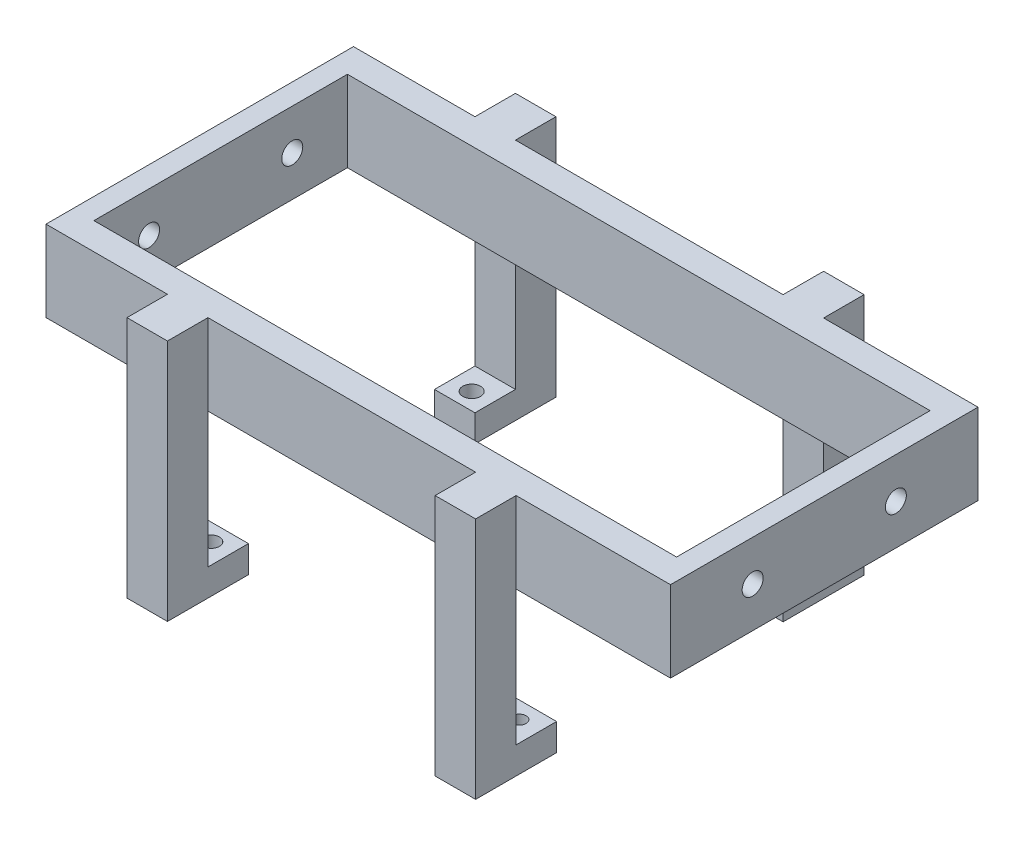
SolidWorks part; units mm, degrees
material "ABS"
ref_plane "Front Plane" through (0, 0, 0) normal (0, 0, 1) x (1, 0, 0)
ref_plane "Top Plane" through (0, 0, 0) normal (0, 1, 0) x (1, 0, 0)
ref_plane "Right Plane" through (0, 0, 0) normal (1, 0, 0) x (0, 0, -1)
sketch "Sketch1" plane through (0, 0, 0) normal (0, 1, 0) x (1, 0, 0)
  line L1 (-58.7693, -28.937) -> (58.7692, -28.937)
  line L2 (-58.7693, -28.937) -> (-58.7693, 28.937)
  line L3 (-58.7693, 28.937) -> (58.7692, 28.937)
  line L4 (58.7692, -28.937) -> (58.7692, 28.937)
  line L5 (-58.7693, -28.937) -> (58.7692, 28.937) construction
  line L6 (-58.7693, 28.937) -> (58.7692, -28.937) construction
  line L7 (-54.8322, -23.8569) -> (54.8323, -23.8569)
  line L8 (-54.8322, -23.8569) -> (-54.8322, 23.857)
  line L9 (-54.8322, 23.857) -> (54.8323, 23.857)
  line L10 (54.8323, -23.8569) -> (54.8323, 23.857)
  line L11 (-54.8322, -23.8569) -> (54.8323, 23.857) construction
  line L12 (-54.8322, 23.857) -> (54.8323, -23.8569) construction
  point P0 (0, 0)
  point P6 (0, 0)
  dimension "D1" = 109.6645
  dimension "D2" = 47.7139
  dimension "D3" = 3.937
  dimension "D4" = 5.08
extrude "Boss-Extrude1" add sketch "Sketch1" along normal blind 15.24
sketch "Sketch2" plane through (58.7692, 0, 0) normal (1, 0, 0) x (0, 0, -1)
  line L0 (-28.937, 15.24) -> (28.937, 15.24) construction
  line L2 (-28.937, 15.24) -> (-28.937, 0) construction
  line L3 (-28.937, 0) -> (28.937, 0) construction
  circle A0 centre (-13.4747, 7.62) radius 1.9749
  circle A1 centre (13.4747, 7.62) radius 1.9749
  point P6 (0, 15.24)
  point P9 (-28.937, 7.62)
  dimension "D3" = 3.9497
  dimension "D4" = 3.9497
  dimension "D1" = 26.9494
  dimension "D2" = 13.4747
  dimension "D5" = 0
  dimension "D6" = 7.62
extrude "Cut-Extrude1" cut sketch "Sketch2" against normal blind 129.032
sketch "Sketch3" plane through (0, 0, 0) normal (0, -1, 0) x (1, 0, 0)
  line L0 (-58.7693, 28.937) -> (58.7692, 28.937) construction
  line L1 (-35.9093, 28.937) -> (-28.2893, 28.937)
  line L2 (-35.9093, 28.937) -> (-35.9093, 36.557)
  line L3 (-35.9093, 36.557) -> (-28.2893, 36.557)
  line L4 (-28.2893, 28.937) -> (-28.2893, 36.557)
  line L7 (22.0907, 28.937) -> (29.7107, 28.937)
  line L8 (22.0907, 28.937) -> (22.0907, 36.557)
  line L9 (22.0907, 36.557) -> (29.7107, 36.557)
  line L10 (29.7107, 28.937) -> (29.7107, 36.557)
  line L11 (-35.9093, -36.557) -> (-28.2893, -36.557)
  line L12 (-35.9093, -36.557) -> (-35.9093, -28.937)
  line L13 (-35.9093, -28.937) -> (-28.2893, -28.937)
  line L14 (-28.2893, -36.557) -> (-28.2893, -28.937)
  line L15 (58.7692, -28.937) -> (-58.7693, -28.937) construction
  line L16 (-58.7693, -28.937) -> (-58.7693, 28.937) construction
  line L17 (22.0907, -28.937) -> (29.7107, -28.937)
  line L18 (22.0907, -28.937) -> (22.0907, -36.557)
  line L19 (22.0907, -36.557) -> (29.7107, -36.557)
  line L20 (29.7107, -28.937) -> (29.7107, -36.557)
  point P24 (22.0907, -32.747)
  dimension "D1" = 50.38
  dimension "D2" = 7.62
  dimension "D3" = 7.62
  dimension "D4" = 50.38
  dimension "D5" = 7.62
  dimension "D6" = 7.62
  dimension "D7" = 22.86
  dimension "D8" = 22.86
  dimension "D9" = 7.62
  dimension "D10" = 7.62
  dimension "D11" = 7.62
  dimension "D12" = 7.62
extrude "Boss-Extrude2" add sketch "Sketch3" along normal blind 30.48 and the other way up to surface (15.24 mm away) other way up to face at (0, 15.24, 0)
sketch "Sketch4" plane through (0, -30.48, 0) normal (0, -1, 0) x (1, 0, 0)
  line L0 (-28.2893, -36.557) -> (-35.9093, -36.557) construction
  line L1 (-35.9093, 28.937) -> (-28.2893, 28.937)
  line L2 (-35.9093, 28.937) -> (-35.9093, 21.317)
  line L3 (-35.9093, 21.317) -> (-28.2893, 21.317)
  line L4 (-28.2893, 28.937) -> (-28.2893, 21.317)
  line L5 (22.0907, 28.937) -> (29.7107, 28.937)
  line L6 (22.0907, 28.937) -> (22.0907, 21.317)
  line L7 (22.0907, 21.317) -> (29.7107, 21.317)
  line L8 (29.7107, 28.937) -> (29.7107, 21.317)
  line L9 (-35.9093, -28.937) -> (-28.2893, -28.937)
  line L10 (-35.9093, -28.937) -> (-35.9093, -21.317)
  line L11 (-35.9093, -21.317) -> (-28.2893, -21.317)
  line L12 (-28.2893, -28.937) -> (-28.2893, -21.317)
  line L13 (29.7107, -28.937) -> (22.0907, -28.937)
  line L14 (29.7107, -28.937) -> (29.7107, -21.317)
  line L15 (29.7107, -21.317) -> (22.0907, -21.317)
  line L16 (22.0907, -28.937) -> (22.0907, -21.317)
  line L17 (29.7107, -36.557) -> (22.0907, -36.557) construction
  line L18 (22.0907, 36.557) -> (29.7107, 36.557) construction
  line L19 (-35.9093, 36.557) -> (-28.2893, 36.557) construction
  line L20 (-28.2893, -28.937) -> (-35.9093, -28.937) construction
  line L21 (-28.2893, 28.937) -> (-28.2893, 36.557) construction
  line L22 (-35.9093, 28.937) -> (-28.2893, 28.937) construction
  line L23 (22.0907, -28.937) -> (22.0907, -36.557) construction
  line L24 (29.7107, -28.937) -> (22.0907, -28.937) construction
  circle A0 centre (-32.0993, 24.511) radius 1.5453
  circle A1 centre (25.9007, 24.511) radius 1.269
  circle A2 centre (25.9007, -24.511) radius 1.7336
  circle A3 centre (-32.0993, -24.511) radius 1.6712
  point P37 (25.9007, 28.937)
  dimension "D5" = 15.24
  dimension "D6" = 15.24
  dimension "D7" = 15.24
  dimension "D8" = 15.24
  dimension "D9" = 3.81
  dimension "D10" = 3.81
  dimension "D11" = 3.81
  dimension "D12" = 3.81
  dimension "D13" = 49.022
  dimension "D14" = 49.022
  dimension "D15" = 4.4259
  dimension "D16" = 4.4259
extrude "Boss-Extrude3" add sketch "Sketch4" against normal blind 5.08
